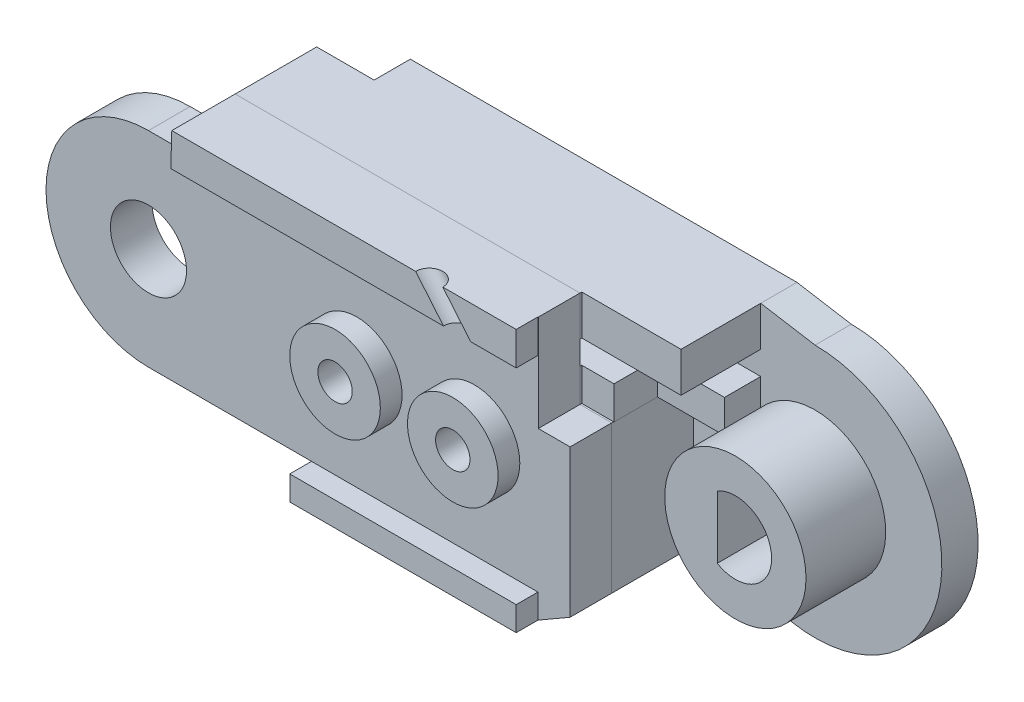
SolidWorks part; units mm, degrees
ref_plane "Front Plane" through (0, 0, 0) normal (0, 0, 1) x (1, 0, 0)
ref_plane "Top Plane" through (0, 0, 0) normal (0, 1, 0) x (1, 0, 0)
ref_plane "Right Plane" through (0, 0, 0) normal (1, 0, 0) x (0, 0, -1)
sketch "Sketch3" plane through (0, 0, 0) normal (0, 0, 1) x (1, 0, 0)
  line L7 (8, 0) -> (9, -2.5)
  line L11 (30, 7) -> (27, 7.5)
  line L13 (0, 7) -> (0, 7.5) construction
  line L14 (0, 7.5) -> (-22.3287, 7.5) construction
  line L15 (0, 5.3) -> (-14, 5.3) construction
  line L16 (0, 4) -> (-14, 4) construction
  line L17 (-14, 4) -> (-14, 5.3) construction
  line L18 (5.6569, 5.6569) -> (5.6569, 7.5)
  line L19 (5.6569, 7.5) -> (27, 7.5)
  line L20 (21.5, -7) -> (9, -7)
  line L21 (9, -7) -> (9, -2.5)
  line L23 (25.0503, -4.9497) -> (21.5, -7)
  arc A4 (8, 0) -> (5.6569, 5.6569) centre (0, 0) ccw
  arc A5 (25.0503, -4.9497) -> (30, 7) centre (30, 0) ccw
  circle A6 centre (0, 0) radius 7 construction
  circle A7 centre (0, 0) radius 3.9 construction
  circle A8 centre (0, 0) radius 5.3 construction
  circle A9 centre (0, 0) radius 4 construction
  dimension "D10" = 0.5
  dimension "D17" = 14
  dimension "D5" = 135
  dimension "D6" = 12.5
  dimension "D7" = 4.5
  dimension "D8" = 1
  dimension "D9" = 45
  dimension "D11" = 1.8431
  dimension "D12" = 30
  dimension "D14" = 3
extrude "Boss-Extrude1" add sketch "Sketch3" along normal blind 2 contours A5 L11 L19 L18 A4 L7 L21 L20 L23
sketch "Sketch20" plane through (0, 0, 0) normal (0, 0, 1) x (1, 0, 0)
  line L0 (0, 7) -> (0, 7.5) construction
  line L1 (0, 7.5) -> (-19.4737, 7.5) construction
  line L2 (0, 5.3) -> (-14, 5.3) construction
  line L3 (0, 4) -> (-14, 4) construction
  line L4 (-14, 4) -> (-14, 5.3) construction
  line L5 (0, 5.3) -> (17.4849, 5.3) construction
  line L6 (17.4849, 5.3) -> (17.4849, 4) construction
  line L7 (17.4849, 4) -> (0, 4) construction
  line L8 (-2.5, 7.5) -> (-2.5, 2.868) construction
  circle A0 centre (0, 0) radius 7 construction
  circle A1 centre (0, 0) radius 3.9 construction
  circle A3 centre (0, 0) radius 5.3 construction
  circle A4 centre (0, 0) radius 4 construction
  circle A5 centre (0, 0) radius 2 construction
  dimension "D1" = 0
  dimension "D2" = 2.5
ref_plane "Plane1" through (0, 0, 2) normal (0, 0, 1) x (1, 0, 0)
sketch "Sketch4" plane through (0, 0, 2) normal (0, 0, 1) x (1, 0, 0)
  line L4 (5.6569, 5.6569) -> (5.6569, 7.5)
  line L5 (5.6569, 5.6569) -> (5.6569, 7.5) construction
  line L6 (5.6569, 7.5) -> (21.5, 7.5)
  line L10 (8, 0) -> (9, -2.5)
  line L11 (9, -2.5) -> (9, -7)
  line L12 (9, -7) -> (21.5, -7)
  line L13 (21.5, -7) -> (21.5, 7.5)
  arc A0 (8, 0) -> (5.6569, 5.6569) centre (0, 0) ccw construction
  arc A3 (8, 0) -> (5.6569, 5.6569) centre (0, 0) ccw
sketch "Sketch22" plane through (0, 0, 2) normal (0, 0, 1) x (1, 0, 0)
  line L0 (5.6569, 5.6569) -> (2.4868, 5.6569)
  line L1 (5.6569, 7.5) -> (21.5, 7.5)
  line L2 (5.6569, 7.5) -> (2.4868, 7.5)
  line L3 (2.4868, 7.5) -> (2.4868, 5.6569)
  line L6 (8, 0) -> (9, -2.5)
  line L7 (9, -2.5) -> (9, -7)
  line L8 (9, -7) -> (21.5, -7)
  line L10 (21.5, 7.5) -> (27, 7.5)
  line L11 (27, 7.5) -> (27, 2.172)
  line L12 (27, 2.172) -> (23.2751, 2.172)
  line L13 (21.5, -7) -> (23.2751, -5.9749)
  line L14 (25.0503, -4.9497) -> (21.5, -7) construction
  line L15 (23.2751, -5.9749) -> (23.2751, 2.172)
  arc A0 (8, 0) -> (5.6569, 5.6569) centre (0, 0) ccw
extrude "Boss-Extrude6" add sketch "Sketch22" along normal blind 4.5
sketch "Sketch25" plane through (0, 0, 2) normal (0, 0, 1) x (1, 0, 0)
  line L0 (0, 5.3) -> (18.0981, 5.3) construction
  line L1 (0, 4) -> (18.0981, 4) construction
  line L2 (18.0981, 4) -> (18.0981, 5.3) construction
sketch "Sketch26" plane through (0, 0, 2) normal (0, 0, 1) x (1, 0, 0)
  line L1 (18.0981, 5.3) -> (2.5301, 5.3)
  line L2 (18.0981, 4) -> (2.5301, 4)
  line L3 (2.5301, 5.3) -> (2.5301, 4)
  line L4 (18.0981, 5.3) -> (27, 5.3)
  line L5 (27, 2.172) -> (27, 7.5) construction
  line L6 (27, 5.3) -> (27, 4)
  line L7 (27, 4) -> (18.0981, 4)
extrude "Cut-Extrude6" cut sketch "Sketch26" along normal blind 4.5
ref_plane "Plane18" through (0, 0, 6.5) normal (0, 0, 1) x (1, 0, 0)
sketch "Sketch31" plane through (0, 0, 6.5) normal (0, 0, 1) x (1, 0, 0)
  line L0 (2.4327, 5.6569) -> (0, 5.6569)
  line L4 (9, -5.6569) -> (0, -5.6569)
  line L5 (2.4327, 5.6569) -> (2.4868, 7.5)
  line L12 (9, -7) -> (9, -5.6569)
  line L13 (9, -2.5) -> (9, -7) construction
  line L16 (27, 7.5) -> (27, 2.172)
  line L17 (27, 2.172) -> (23.2751, 2.172)
  line L18 (23.2751, -5.9749) -> (23.2751, 2.172)
  line L19 (27, 7.5) -> (2.4868, 7.5)
  line L20 (9, -7) -> (21.5, -7)
  line L21 (21.5, -7) -> (23.2751, -5.9749)
  arc A0 (0, 5.6569) -> (0, -5.6569) centre (0, 0) ccw
  dimension "D1" = 5.6569
extrude "Boss-Extrude14" add sketch "Sketch31" along normal blind 2.3 separate body
sketch "Sketch32" plane through (0, 0, 8.8) normal (0, 0, 1) x (1, 0, 0)
  circle A0 centre (0, 0) radius 2.1
extrude "Cut-Extrude7" cut sketch "Sketch32" against normal blind 2.3
sketch "Sketch33" plane through (0, 0, 8.8) normal (0, 0, 1) x (1, 0, 0)
  line L4 (9, -5.6569) -> (9, -7)
  line L11 (9, -7) -> (21.5, -7)
  line L15 (21.5, -7) -> (21.5, -5.6569)
  line L16 (21.5, -5.6569) -> (9, -5.6569)
  line L17 (2.4868, 7.5) -> (21.5, 7.5)
  line L18 (27, 7.5) -> (2.4868, 7.5) construction
  line L19 (2.4868, 7.5) -> (2.4327, 5.6569)
  line L20 (2.4327, 5.6569) -> (21.5, 5.6569)
  line L21 (21.5, 5.6569) -> (21.5, 7.5)
extrude "Boss-Extrude15" add sketch "Sketch33" along normal blind 1.2
sketch "Sketch34" plane through (0, 0, 2) normal (0, 0, 1) x (1, 0, 0)
  line L0 (30, 5.3) -> (18.0981, 5.3) construction
  line L1 (30, 4) -> (18.0981, 4) construction
  circle A0 centre (30, 0) radius 2 construction
  circle A1 centre (30, 0) radius 5.3 construction
  circle A2 centre (30, 0) radius 4 construction
sketch "Sketch35" plane through (0, 0, 8.8) normal (0, 0, 1) x (1, 0, 0)
  line L0 (27, 2.172) -> (27, 7.5)
  line L1 (27, 2.172) -> (21.5204, 2.172)
  line L2 (27, 7.5) -> (21.5204, 7.5)
  line L3 (21.5204, 2.172) -> (21.5204, 7.5)
  line L4 (27, 2.172) -> (27, 7.5) construction
  line L5 (27, 7.5) -> (21.5, 7.5) construction
  dimension "D1" = 0
extrude "Cut-Extrude8" cut sketch "Sketch35" against normal blind 2.4
sketch "Sketch36" plane through (0, 0, 6.4) normal (0, 0, 1) x (1, 0, 0)
  line L0 (27, 2.172) -> (27, 4)
  line L1 (27, 2.172) -> (23.3, 2.172)
  line L2 (27, 4) -> (23.3, 4)
  line L3 (23.3, 2.172) -> (23.3, 4)
  line L4 (21.5, -7) -> (21.5, 7.5) construction
  dimension "D1" = 1.8
extrude "Cut-Extrude9" cut sketch "Sketch36" against normal blind 2.4
sketch "Sketch37" plane through (0, 0, 2) normal (0, 0, 1) x (1, 0, 0)
  circle A0 centre (30, 0) radius 3.9
extrude "Boss-Extrude16" add sketch "Sketch37" along normal blind 4.4
sketch "Sketch39" plane through (0, 0, 6.4) normal (0, 0, 1) x (1, 0, 0)
  line L0 (29, 1.7321) -> (29, -1.7321)
  arc A0 (29, -1.7321) -> (29, 1.7321) centre (30, 0) ccw
  dimension "D2" = 4
  dimension "D1" = 1
extrude "Cut-Extrude10" cut sketch "Sketch39" against normal through all
sketch "Sketch43" plane through (0, 0, 8.8) normal (0, 0, 1) x (1, 0, 0)
  line L2 (0, -5.6569) -> (9, -5.6569) construction
  circle A0 centre (11.5, 0) radius 2.5
  circle A1 centre (18, 0) radius 2.5
  dimension "D1" = 2.5
  dimension "D3" = 5
  dimension "D4" = 6.5
  dimension "D2" = 5.6569
extrude "Boss-Extrude17" add sketch "Sketch43" along normal blind 1.2
sketch "Sketch44" plane through (0, 0, 10) normal (0, 0, 1) x (1, 0, 0)
  circle A0 centre (11.5, 0) radius 0.95
  circle A1 centre (18, 0) radius 0.95
  dimension "D1" = 1.9
  dimension "D2" = 1.9
extrude "Cut-Extrude11" cut sketch "Sketch44" against normal through all
sketch "Sketch45" plane through (0, 0, 0) normal (0, 0, -1) x (-1, 0, 0)
  circle A0 centre (-11.5, 0) radius 2
  circle A1 centre (-18, 0) radius 2
extrude "Cut-Extrude12" cut sketch "Sketch45" against normal blind 4.5
ref_plane "Plane17" through (0, 0, 10) normal (0, 0, 1) x (1, 0, 0)
sketch "Sketch48" plane through (0, 0, 2) normal (0, 0, 1) x (1, 0, 0)
  circle A0 centre (30, 0) radius 5 construction
sketch "Sketch51" plane through (0, 0, 10) normal (0, 0, 1) x (1, 0, 0)
  line L0 (18.2355, 5.6569) -> (27.0112, -4.8677) construction
  line L1 (2.4327, 5.6569) -> (21.5, 5.6569) construction
sketch "Sketch52" plane through (0, 5.6569, 0) normal (0, -1, 0) x (1, 0, 0)
  circle A0 centre (18.2355, 10) radius 0.75
extrude "Cut-Extrude13" cut sketch "Sketch52" along direction (0.6404, -0.768, 0) on the side against the normal blind 10
